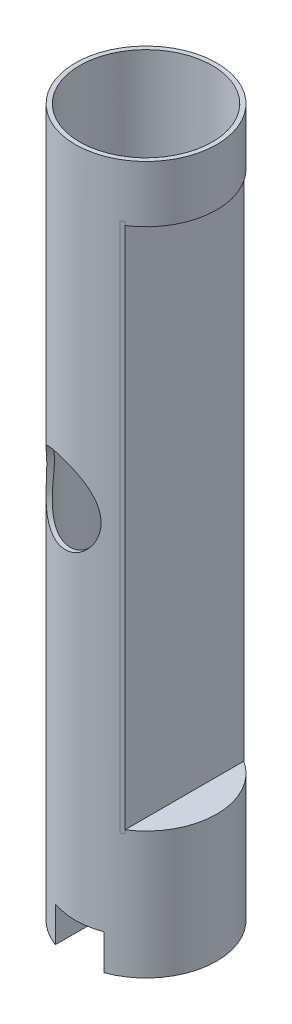
SolidWorks part; units mm, degrees
ref_plane "Front Plane" through (0, 0, 0) normal (0, 0, 1) x (1, 0, 0)
ref_plane "Top Plane" through (0, 0, 0) normal (0, 1, 0) x (1, 0, 0)
ref_plane "Right Plane" through (0, 0, 0) normal (1, 0, 0) x (0, 0, -1)
sketch "Sketch1" plane through (0, 0, 0) normal (0, 1, 0) x (1, 0, 0)
  circle A0 centre (0, 0) radius 50.8
  dimension "D1" = 101.6
extrude "Boss-Extrude1" add sketch "Sketch1" along normal blind 457.2 contours A0
sketch "Sketch2" plane through (0, 457.2, 0) normal (0, 1, 0) x (1, 0, 0)
  circle A0 centre (0, 0) radius 47.625
  dimension "D1" = 95.25
extrude "Cut-Extrude1" cut sketch "Sketch2" against normal through all
sketch "Sketch3" plane through (0, 0, 0) normal (0, 0, 1) x (1, 0, 0)
  line L4 (50.8, 0) -> (50.8, 457.2) construction
  line L5 (50.8, 38.1) -> (25.4, 38.1)
  line L6 (25.4, 38.1) -> (25.4, 419.1)
  line L7 (25.4, 419.1) -> (50.8, 419.1)
  line L8 (50.8, 419.1) -> (50.8, 38.1)
  circle A1 centre (-12.065, 228.6) radius 27.989
extrude "Cut-Extrude3" cut sketch "Sketch3" against normal through all both and the other way through all
sketch "Sketch5" plane through (0, 38.1, 0) normal (0, 1, 0) x (1, 0, 0)
  line L0 (25.4, -43.9941) -> (25.4, 43.9941)
  line L6 (25.4, 43.9941) -> (27.5737, 42.6653)
  line L7 (27.5737, 42.6653) -> (27.5737, -42.6653)
  line L8 (27.5737, -42.6653) -> (25.4, -43.9941)
  circle A5 centre (0, 0) radius 50.8 construction
extrude "Boss-Extrude2" add sketch "Sketch5" along normal blind 381
sketch "Sketch6" plane through (0, 0, 0) normal (0, -1, 0) x (1, 0, 0)
  circle A0 centre (0, 0) radius 50.8
extrude "Boss-Extrude3" add sketch "Sketch6" along normal blind 50.8
sketch "Sketch7" plane through (0, -50.8, 0) normal (0, -1, 0) x (1, 0, 0)
  line L0 (0, -55.88) -> (0, 55.88) construction
  line L1 (17.3746, 47.7364) -> (17.3746, 22.1168)
  line L2 (17.3746, 22.1168) -> (-17.3746, 22.1168)
  line L3 (-17.3746, 22.1168) -> (-17.3746, 47.7364)
  line L4 (55.88, 0) -> (-55.88, 0) construction
  line L5 (17.3746, -22.1168) -> (-17.3746, -22.1168)
  line L6 (17.3746, -47.7364) -> (17.3746, -22.1168)
  line L7 (-17.3746, -22.1168) -> (-17.3746, -47.7364)
  arc A0 (0, 50.8) -> (17.3746, 47.7364) centre (0, 0) cw
  circle A1 centre (0, 0) radius 50.8 construction
  arc A2 (0, 50.8) -> (-17.3746, 47.7364) centre (0, 0) ccw
  arc A3 (0, -50.8) -> (-17.3746, -47.7364) centre (0, 0) cw
  arc A4 (0, -50.8) -> (17.3746, -47.7364) centre (0, 0) ccw
extrude "Cut-Extrude4" cut sketch "Sketch7" against normal blind 25.4
sketch "Sketch8" plane through (0, 0, 22.1168) normal (0, 0, 1) x (1, 0, 0)
  line L2 (0, -55.88) -> (0, 55.88) construction
  circle A0 centre (0, -38.0915) radius 3.302
extrude "Cut-Extrude5" cut sketch "Sketch8" against normal through all
sketch "Sketch9" plane through (0, 38.1, 0) normal (0, 1, 0) x (1, 0, 0)
  line L0 (27.5737, 42.6653) -> (27.5737, -42.6653)
  arc A0 (27.5737, -42.6653) -> (27.5737, 42.6653) centre (0, 0) ccw
  circle A1 centre (0, 0) radius 50.8 construction
extrude "Boss-Extrude4" add sketch "Sketch9" along normal blind 2.54
sketch "Sketch10" plane through (0, 419.1, 0) normal (0, -1, 0) x (1, 0, 0)
  line L0 (27.5737, 42.6653) -> (27.5737, -42.6653)
  arc A0 (27.5737, -42.6653) -> (27.5737, 42.6653) centre (0, 0) ccw
extrude "Boss-Extrude5" add sketch "Sketch10" along normal blind 2.54
sketch "Sketch13" plane through (0, 457.2, 0) normal (0, 1, 0) x (1, 0, 0)
  circle A0 centre (0, 0) radius 47.625
curve "Helix/Spiral1" pitch 5.08 height 15.24 turns 3
sketch "Sketch14" plane through (0, 0, 0) normal (1, 0, 0) x (0, 0, -1)
  line L0 (-50.8, 457.2) -> (-50.8, 504.2078) construction
  line L5 (-47.6405, 479.4205) -> (-47.6193, 481.7669)
  line L6 (-47.6193, 481.7669) -> (-49.6619, 480.6121)
  line L7 (-49.6619, 480.6121) -> (-47.6405, 479.4205)
  circle A0 centre (-48.3072, 480.5999) radius 0.6774
  point P9 (-47.6299, 480.5937)
  dimension "D1" = 2.032
sketch "Sketch25" plane through (0, 0, 0) normal (1, 0, 0) x (0, 0, -1)
  line L0 (-47.625, 457.2) -> (-47.625, 503.4405) construction
sketch "Sketch26" plane through (0, -50.8, 0) normal (0, -1, 0) x (1, 0, 0)
  line L1 (6.35, 9.525) -> (-6.35, 9.525)
  line L2 (6.35, 9.525) -> (6.35, -9.525)
  line L3 (6.35, -9.525) -> (-6.35, -9.525)
  line L4 (-6.35, 9.525) -> (-6.35, -9.525)
  line L5 (6.35, 9.525) -> (-6.35, -9.525) construction
  line L6 (6.35, -9.525) -> (-6.35, 9.525) construction
  point P0 (0, 0)
  dimension "D1" = 12.7
  dimension "D2" = 19.05
extrude "Cut-Extrude6" cut sketch "Sketch26" against normal blind 84.582
